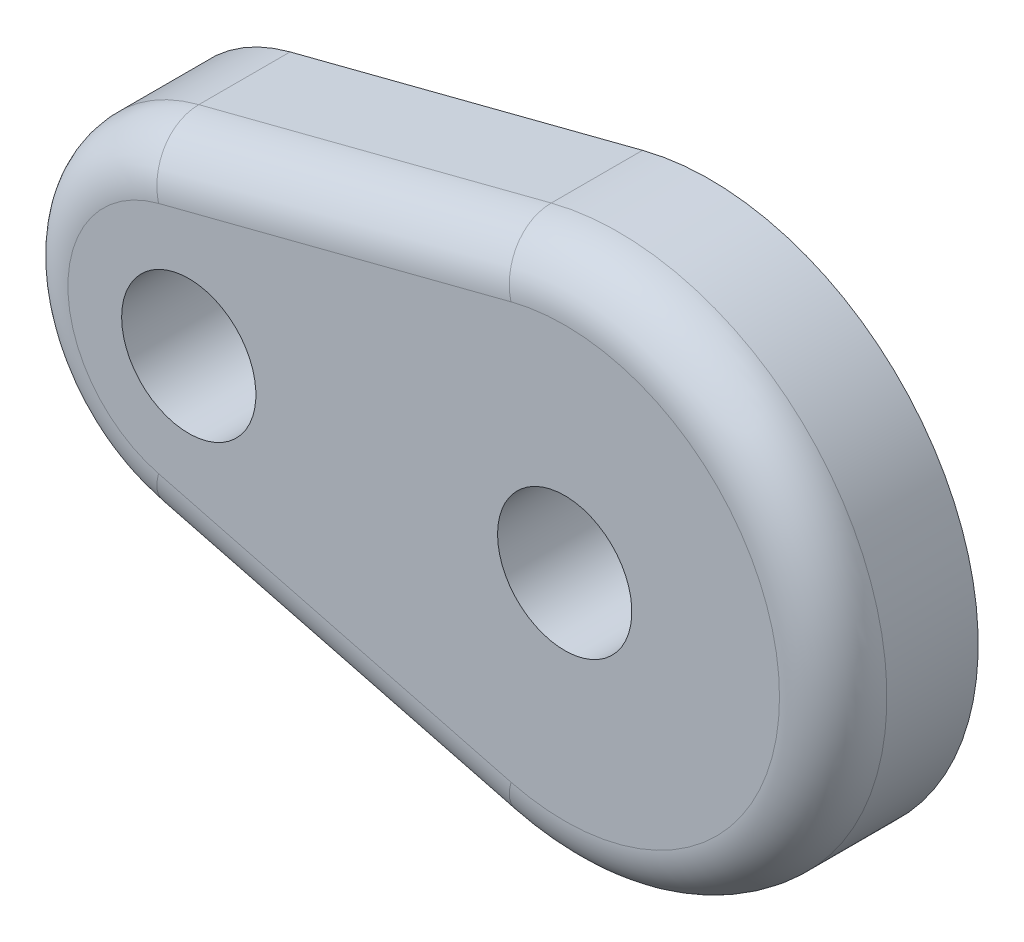
SolidWorks part; units mm, degrees
ref_plane "Front Plane" through (0, 0, 0) normal (0, 0, 1) x (1, 0, 0)
ref_plane "Top Plane" through (0, 0, 0) normal (0, 1, 0) x (1, 0, 0)
ref_plane "Right Plane" through (0, 0, 0) normal (1, 0, 0) x (0, 0, -1)
sketch "Sketch1" plane through (0, 0, 0) normal (0, 0, 1) x (1, 0, 0)
  line L0 (-9.9219, 3.9964) -> (-1.5875, 6.1484)
  line L1 (-9.9219, -3.9964) -> (-1.5875, -6.1484)
  arc A0 (-1.5875, -6.1484) -> (-1.5875, 6.1484) centre (0, 0) ccw
  circle A1 centre (-8.89, 0) radius 1.5875 construction
  arc A2 (-9.9219, 3.9964) -> (-9.9219, -3.9964) centre (-8.89, 0) ccw
  dimension "D1" = 12.7
  dimension "D3" = 3.175
  dimension "D4" = 8.255
  dimension "D2" = 8.89
extrude "Boss-Extrude1" add sketch "Sketch1" along normal blind 4.7625 contours L0 A0 L1 A2
sketch "Sketch2" plane through (0, 0, 0) normal (0, 0, -1) x (-1, 0, 0)
  line L2 (9.9219, 3.9964) -> (1.5875, 6.1484)
  line L3 (1.5875, -6.1484) -> (9.9219, -3.9964)
  line L4 (9.9219, 3.9964) -> (1.5875, 6.1484)
  line L5 (1.5875, -6.1484) -> (9.9219, -3.9964)
  arc A2 (9.9219, -3.9964) -> (9.9219, 3.9964) centre (8.89, 0) ccw
  arc A3 (1.5875, 6.1484) -> (1.5875, -6.1484) centre (0, 0) ccw
  arc A4 (9.9219, -3.9964) -> (9.9219, 3.9964) centre (8.89, 0) ccw
  arc A5 (1.5875, 6.1484) -> (1.5875, -6.1484) centre (0, 0) ccw
  dimension "D1" = 0
extrude "Cut-Extrude1" cut sketch "Sketch2" against normal offset from surface (1.3335 mm away) 0.127
hole_wizard "1/8 (0.1250) Dowel Hole1" positions "Sketch3" profile "Sketch4" hole size "1/8" standard "ANSI Inch" end condition through all
sketch "Sketch3" plane through (0, 0, 1.3335) normal (0, 0, -1) x (-1, 0, 0)
  point P0 (8.89, 0)
  point P4 (0, 0)
sketch "Sketch4" plane through (-8.89, 0, 1.3335) normal (1, 0, 0) x (0, 1, 0)
  line L0 (0, 0) -> (0, 3.429)
  line L1 (0, 3.429) -> (1.5875, 3.429)
  line L2 (1.5875, 3.429) -> (1.5875, 0)
  line L5 (1.5875, 0) -> (0, 0)
  line L11 (0, -6.35) -> (0, 107.95) construction
  dimension "Thru Hole Dia." = 3.175
  dimension "Thru Hole Depth" = 3.429
fillet "Fillet1" radius 1.27 4 edges at (-13.0175, 0, 4.7625) (-5.7547, -5.0724, 4.7625) (6.35, 0, 4.7625) (-5.7547, 5.0724, 4.7625)
